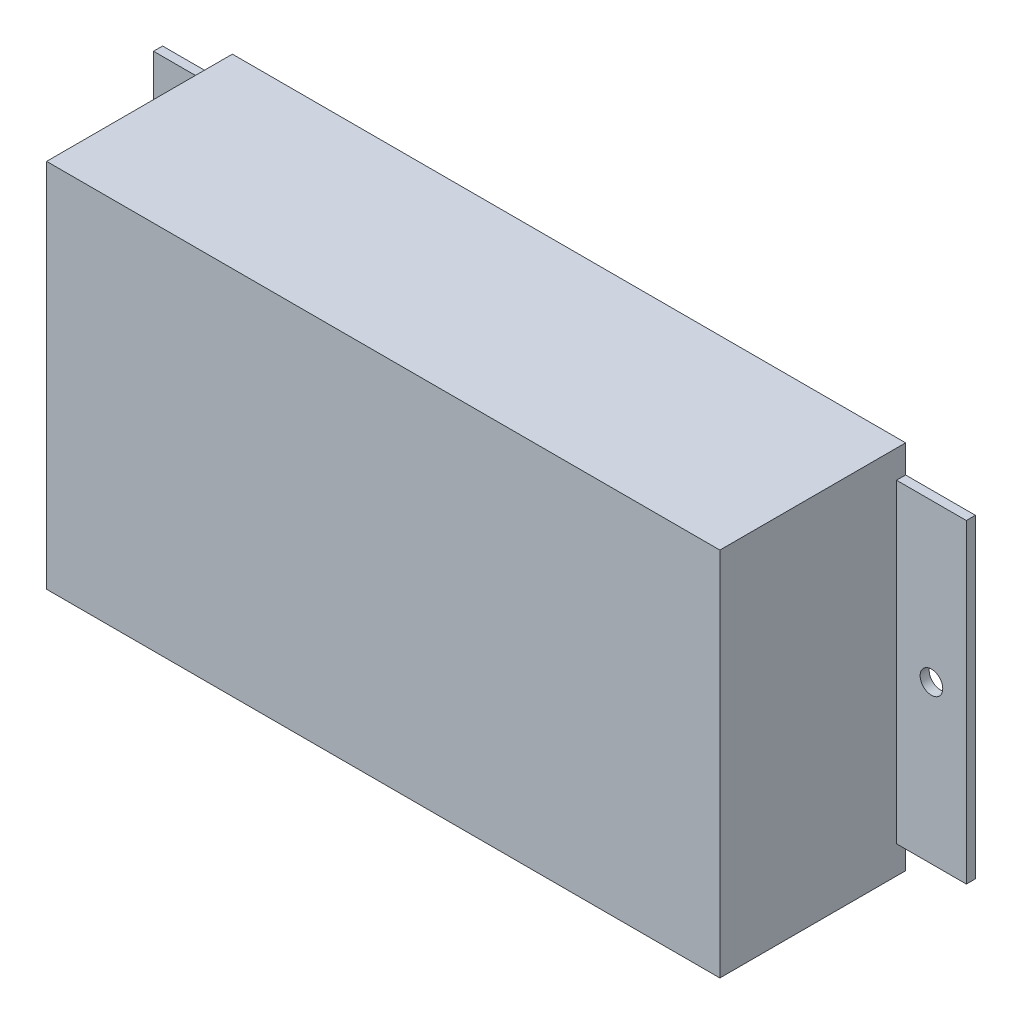
SolidWorks part; units mm, degrees
ref_plane "Front Plane" through (0, 0, 0) normal (0, 0, 1) x (1, 0, 0)
ref_plane "Top Plane" through (0, 0, 0) normal (0, 1, 0) x (1, 0, 0)
ref_plane "Right Plane" through (0, 0, 0) normal (1, 0, 0) x (0, 0, -1)
sketch "Sketch1" plane through (0, 0, 0) normal (0, 0, 1) x (1, 0, 0)
  line L1 (0, 0) -> (148.6, 0)
  line L2 (0, 0) -> (0, -81.8)
  line L3 (0, -81.8) -> (148.6, -81.8)
  line L4 (148.6, 0) -> (148.6, -81.8)
  dimension "D1" = 81.8
  dimension "D2" = 148.6
extrude "Boss-Extrude1" add sketch "Sketch1" along normal blind 41
sketch "Sketch2" plane through (0, 0, 0) normal (0, 0, -1) x (-1, 0, 0)
  line L0 (0, 0) -> (0, -81.8) construction
  line L1 (0, -6.15) -> (15.4, -6.15)
  line L2 (0, -6.15) -> (0, -75.65)
  line L3 (0, -75.65) -> (15.4, -75.65)
  line L4 (15.4, -6.15) -> (15.4, -75.65)
  line L5 (-74.3, 0) -> (-74.3, -93.5562) construction
  line L6 (-148.6, 0) -> (0, 0) construction
  line L7 (-148.6, -75.65) -> (-164, -75.65)
  line L8 (-164, -6.15) -> (-164, -75.65)
  line L9 (-148.6, -6.15) -> (-164, -6.15)
  line L10 (-148.6, -6.15) -> (-148.6, -75.65)
  line L11 (-156.3, -40.9) -> (7.7, -40.9) construction
  circle A0 centre (7.7, -40.9) radius 2.5
  circle A1 centre (-156.3, -40.9) radius 2.5
  dimension "D4" = 5
  dimension "D5" = 7.7
  dimension "D6" = 34.75
  dimension "D1" = 69.5
  dimension "D2" = 15.4
  dimension "D3" = 6.15
extrude "Boss-Extrude2" add sketch "Sketch2" against normal blind 2
